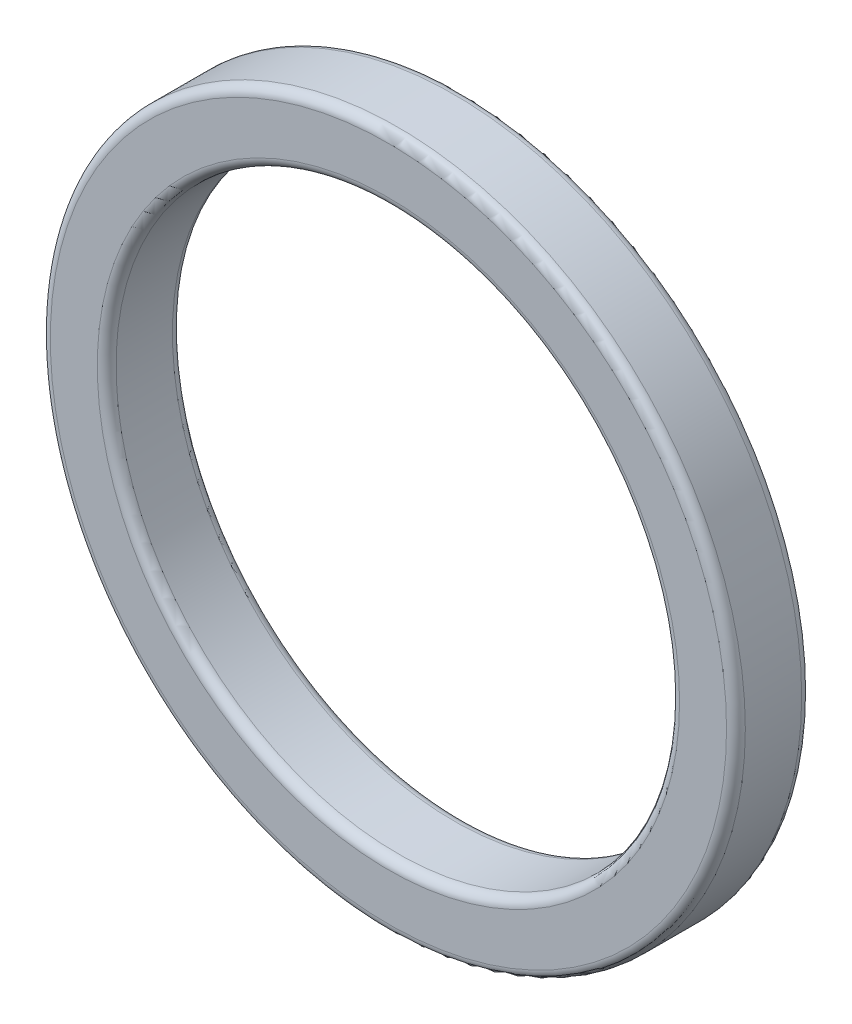
SolidWorks part; units mm, degrees
ref_plane "前视基准面" through (0, 0, 0) normal (0, 0, 1) x (1, 0, 0)
ref_plane "上视基准面" through (0, 0, 0) normal (0, 1, 0) x (1, 0, 0)
ref_plane "右视基准面" through (0, 0, 0) normal (1, 0, 0) x (0, 0, -1)
sketch "草图1" plane through (0, 0, 0) normal (0, 0, 1) x (1, 0, 0)
  circle A0 centre (0, 0) radius 15
  circle A1 centre (0, 0) radius 18.5
  dimension "D1" = 30
  dimension "D2" = 37
extrude "凸台-拉伸1" add sketch "草图1" along normal blind 4
fillet "圆角1" radius 0.5 4 edges at (15, 0, 0) (15, 0, 4) (18.5, 0, 0) (18.5, 0, 4)
